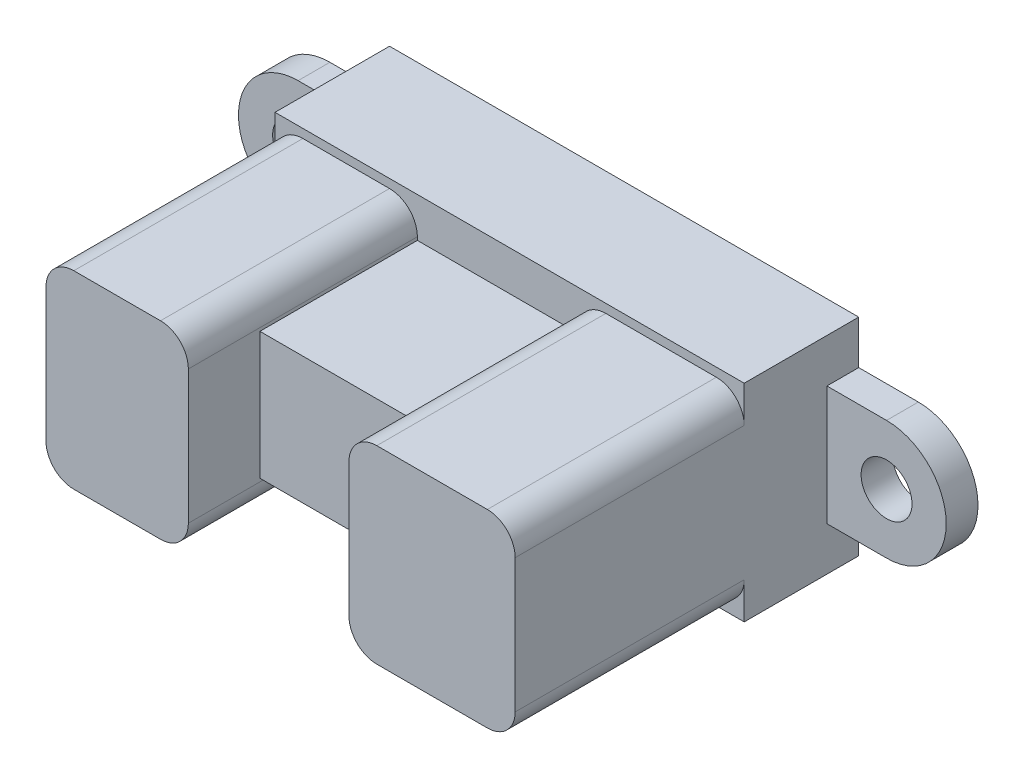
SolidWorks part; units mm, degrees
ref_plane "Alzado" through (0, 0, 0) normal (0, 0, 1) x (1, 0, 0)
ref_plane "Planta" through (0, 0, 0) normal (0, 1, 0) x (1, 0, 0)
ref_plane "Vista lateral" through (0, 0, 0) normal (1, 0, 0) x (0, 0, -1)
sketch "Croquis1" plane through (0, 0, 0) normal (0, 0, 1) x (1, 0, 0)
  line L1 (18.5, -3.75) -> (-18.5, -3.75)
  line L2 (18.5, -3.75) -> (18.5, 3.75) construction
  line L3 (18.5, 3.75) -> (-18.5, 3.75)
  line L4 (-18.5, -3.75) -> (-18.5, 3.75) construction
  line L5 (18.5, -3.75) -> (-18.5, 3.75) construction
  line L6 (18.5, 3.75) -> (-18.5, -3.75) construction
  arc A0 (-18.5, -3.75) -> (-18.5, 3.75) centre (-18.5, 0) cw
  arc A1 (18.5, 3.75) -> (18.5, -3.75) centre (18.5, 0) cw
  circle A2 centre (-18.5, 0) radius 1.6
  circle A3 centre (18.5, 0) radius 1.6
  point P0 (0, 0)
  dimension "D3" = 3.2
  dimension "D1" = 37
  dimension "D2" = 7.5
extrude "Saliente-Extruir1" add sketch "Croquis1" along normal blind 2
sketch "Croquis2" plane through (0, 0, 0) normal (0, 0, 1) x (1, 0, 0)
  line L1 (14.75, -6.5) -> (-14.75, -6.5)
  line L2 (14.75, -6.5) -> (14.75, 6.5)
  line L3 (14.75, 6.5) -> (-14.75, 6.5)
  line L4 (-14.75, -6.5) -> (-14.75, 6.5)
  line L5 (14.75, -6.5) -> (-14.75, 6.5) construction
  line L6 (14.75, 6.5) -> (-14.75, -6.5) construction
  point P0 (0, 0)
  dimension "D1" = 29.5
  dimension "D2" = 13
extrude "Saliente-Extruir2" add sketch "Croquis2" along normal blind 7.2
sketch "Croquis3" plane through (0, 0, 7.2) normal (0, 0, 1) x (1, 0, 0)
  line L0 (-14.75, 6.5) -> (-14.75, -6.5) construction
  line L1 (-7.55, 5.95) -> (-13, 5.95)
  line L2 (-5.8, 4.2) -> (-5.8, -4.2)
  line L3 (-7.55, -5.95) -> (-13, -5.95)
  line L4 (-14.75, 4.2) -> (-14.75, -4.2)
  line L5 (-5.8, 5.95) -> (-14.75, -5.95) construction
  line L6 (-5.8, -5.95) -> (-14.75, 5.95) construction
  line L7 (14.75, -6.5) -> (14.75, 6.5) construction
  line L8 (6.05, 5.95) -> (13, 5.95)
  line L9 (4.3, 4.2) -> (4.3, -4.2)
  line L10 (6.05, -5.95) -> (13, -5.95)
  line L11 (14.75, 4.2) -> (14.75, -4.2)
  line L12 (4.3, 5.95) -> (14.75, -5.95) construction
  line L13 (4.3, -5.95) -> (14.75, 5.95) construction
  line L14 (0, 0) -> (0, 4) construction
  line L15 (-5.8, 4) -> (4.3, 4)
  line L16 (-5.8, 4) -> (-5.8, -4)
  line L17 (-5.8, -4) -> (4.3, -4)
  line L18 (4.3, 4) -> (4.3, -4)
  line L21 (0, -4) -> (0, 0) construction
  line L22 (9.525, 0) -> (0, 0) construction
  line L23 (0, 0) -> (-10.275, 0) construction
  arc A0 (-13, 5.95) -> (-14.75, 4.2) centre (-13, 4.2) ccw
  arc A1 (-13, -5.95) -> (-14.75, -4.2) centre (-13, -4.2) cw
  arc A2 (13, -5.95) -> (14.75, -4.2) centre (13, -4.2) ccw
  arc A3 (13, 5.95) -> (14.75, 4.2) centre (13, 4.2) cw
  arc A4 (6.05, 5.95) -> (4.3, 4.2) centre (6.05, 4.2) ccw
  arc A5 (4.3, -4.2) -> (6.05, -5.95) centre (6.05, -4.2) ccw
  arc A6 (-5.8, -4.2) -> (-7.55, -5.95) centre (-7.55, -4.2) cw
  arc A7 (-7.55, 5.95) -> (-5.8, 4.2) centre (-7.55, 4.2) cw
  point P0 (-10.275, 0)
  point P7 (9.525, 0)
  line M1 (-14.75, 6.5) -> (-14.75, -6.5)
  line M3 (14.75, -6.5) -> (14.75, 6.5)
  dimension "D5" = 1.75
  dimension "D1" = 10.45
  dimension "D2" = 8.95
  dimension "D3" = 11.9
  dimension "D4" = 8
extrude "Saliente-Extruir3" add sketch "Croquis3" along normal blind 9.9 contours A7 L1 A0 A1 L3 A6 L2 M1 | L2 L17 L9 L15 | L9 A5 L10 A2 A3 L8 A4 M3
sketch "Croquis4" plane through (0, 0, 17.1) normal (0, 0, 1) x (1, 0, 0)
  line L0 (-5.8, -4) -> (-5.8, 4)
  line L1 (4.3, 4) -> (4.3, -4)
  line L12 (-7.55, 5.95) -> (-13, 5.95)
  line L13 (-14.75, 4.2) -> (-14.75, -4.2)
  line L14 (-13, -5.95) -> (-7.55, -5.95)
  line L15 (-5.8, -4.2) -> (-5.8, -4)
  line L16 (-5.8, -4) -> (4.3, -4)
  line L17 (4.3, -4) -> (4.3, -4.2)
  line L18 (6.05, -5.95) -> (13, -5.95)
  line L19 (14.75, -4.2) -> (14.75, 4.2)
  line L20 (13, 5.95) -> (6.05, 5.95)
  line L21 (4.3, 4.2) -> (4.3, 4)
  line L22 (4.3, 4) -> (-5.8, 4)
  line L23 (-5.8, 4) -> (-5.8, 4.2)
  line L24 (-7.55, 5.95) -> (-13, 5.95)
  line L25 (-14.75, 4.2) -> (-14.75, -4.2)
  line L26 (-13, -5.95) -> (-7.55, -5.95)
  line L27 (-5.8, -4.2) -> (-5.8, -4)
  line L28 (-5.8, -4) -> (4.3, -4)
  line L29 (4.3, -4) -> (4.3, -4.2)
  line L30 (6.05, -5.95) -> (13, -5.95)
  line L31 (14.75, -4.2) -> (14.75, 4.2)
  line L32 (13, 5.95) -> (6.05, 5.95)
  line L33 (4.3, 4.2) -> (4.3, 4)
  line L34 (4.3, 4) -> (-5.8, 4)
  line L35 (-5.8, 4) -> (-5.8, 4.2)
  arc A8 (-5.8, 4.2) -> (-7.55, 5.95) centre (-7.55, 4.2) ccw
  arc A9 (-13, 5.95) -> (-14.75, 4.2) centre (-13, 4.2) ccw
  arc A10 (-14.75, -4.2) -> (-13, -5.95) centre (-13, -4.2) ccw
  arc A11 (-7.55, -5.95) -> (-5.8, -4.2) centre (-7.55, -4.2) ccw
  arc A12 (4.3, -4.2) -> (6.05, -5.95) centre (6.05, -4.2) ccw
  arc A13 (13, -5.95) -> (14.75, -4.2) centre (13, -4.2) ccw
  arc A14 (14.75, 4.2) -> (13, 5.95) centre (13, 4.2) ccw
  arc A15 (6.05, 5.95) -> (4.3, 4.2) centre (6.05, 4.2) ccw
  arc A16 (-5.8, 4.2) -> (-7.55, 5.95) centre (-7.55, 4.2) ccw
  arc A17 (-13, 5.95) -> (-14.75, 4.2) centre (-13, 4.2) ccw
  arc A18 (-14.75, -4.2) -> (-13, -5.95) centre (-13, -4.2) ccw
  arc A19 (-7.55, -5.95) -> (-5.8, -4.2) centre (-7.55, -4.2) ccw
  arc A20 (4.3, -4.2) -> (6.05, -5.95) centre (6.05, -4.2) ccw
  arc A21 (13, -5.95) -> (14.75, -4.2) centre (13, -4.2) ccw
  arc A22 (14.75, 4.2) -> (13, 5.95) centre (13, 4.2) ccw
  arc A23 (6.05, 5.95) -> (4.3, 4.2) centre (6.05, 4.2) ccw
  arc M21 (-5.8, 4.2) -> (-7.55, 5.95) centre (-7.55, 4.2) ccw
  line M22 (-7.55, 5.95) -> (-13, 5.95)
  arc M23 (-13, 5.95) -> (-14.75, 4.2) centre (-13, 4.2) ccw
  line M24 (-14.75, 4.2) -> (-14.75, -4.2)
  arc M25 (-14.75, -4.2) -> (-13, -5.95) centre (-13, -4.2) ccw
  line M26 (-13, -5.95) -> (-7.55, -5.95)
  arc M27 (-7.55, -5.95) -> (-5.8, -4.2) centre (-7.55, -4.2) ccw
  line M28 (-5.8, -4.2) -> (-5.8, -4)
  line M30 (4.3, -4) -> (4.3, -4.2)
  arc M31 (4.3, -4.2) -> (6.05, -5.95) centre (6.05, -4.2) ccw
  line M32 (6.05, -5.95) -> (13, -5.95)
  arc M33 (13, -5.95) -> (14.75, -4.2) centre (13, -4.2) ccw
  line M34 (14.75, -4.2) -> (14.75, 4.2)
  arc M35 (14.75, 4.2) -> (13, 5.95) centre (13, 4.2) ccw
  line M36 (13, 5.95) -> (6.05, 5.95)
  arc M37 (6.05, 5.95) -> (4.3, 4.2) centre (6.05, 4.2) ccw
  line M38 (4.3, 4.2) -> (4.3, 4)
  line M40 (-5.8, 4) -> (-5.8, 4.2)
  dimension "D1" = 0
extrude "Saliente-Extruir4" add sketch "Croquis4" along normal blind 4.5 contours L0 M28 M40 M21 M22 M23 M24 M25 M26 M27 | L1 M38 M30 M31 M32 M33 M34 M35 M36 M37
sketch "Croquis5" plane through (0, -6.5, 0) normal (0, -1, 0) x (1, 0, 0)
  line L0 (-14.75, 0) -> (14.75, 0) construction
  line L1 (5.05, 3.3) -> (-5.05, 3.3)
  line L2 (5.05, 3.3) -> (5.05, 4.5)
  line L3 (5.05, 4.5) -> (-5.05, 4.5)
  line L4 (-5.05, 3.3) -> (-5.05, 4.5)
  line L5 (5.05, 3.3) -> (-5.05, 4.5) construction
  line L6 (5.05, 4.5) -> (-5.05, 3.3) construction
  line L7 (0, 3.9) -> (0, 0) construction
  point P0 (0, 3.9)
  dimension "D1" = 3.3
  dimension "D2" = 1.2
  dimension "D3" = 10.1
extrude "Saliente-Extruir5" add sketch "Croquis5" along normal blind 6
sketch "Croquis6" plane through (0, -6.5, 0) normal (0, -1, 0) x (1, 0, 0)
  line L0 (5.05, 4.5) -> (-5.05, 4.5) construction
  line L1 (4, 9.3) -> (-4, 9.3)
  line L2 (4, 9.3) -> (4, 4.5)
  line L3 (4, 4.5) -> (-4, 4.5)
  line L4 (-4, 9.3) -> (-4, 4.5)
  line L5 (4, 9.3) -> (-4, 4.5) construction
  line L6 (4, 4.5) -> (-4, 9.3) construction
  line L7 (-5.05, 3.3) -> (5.05, 3.3) construction
  line L8 (0, 0) -> (0, 6.9) construction
  line L9 (-14.75, 0) -> (14.75, 0) construction
  point P0 (0, 6.9)
  dimension "D1" = 6
  dimension "D2" = 8
extrude "Saliente-Extruir6" add sketch "Croquis6" along normal blind 5.9
